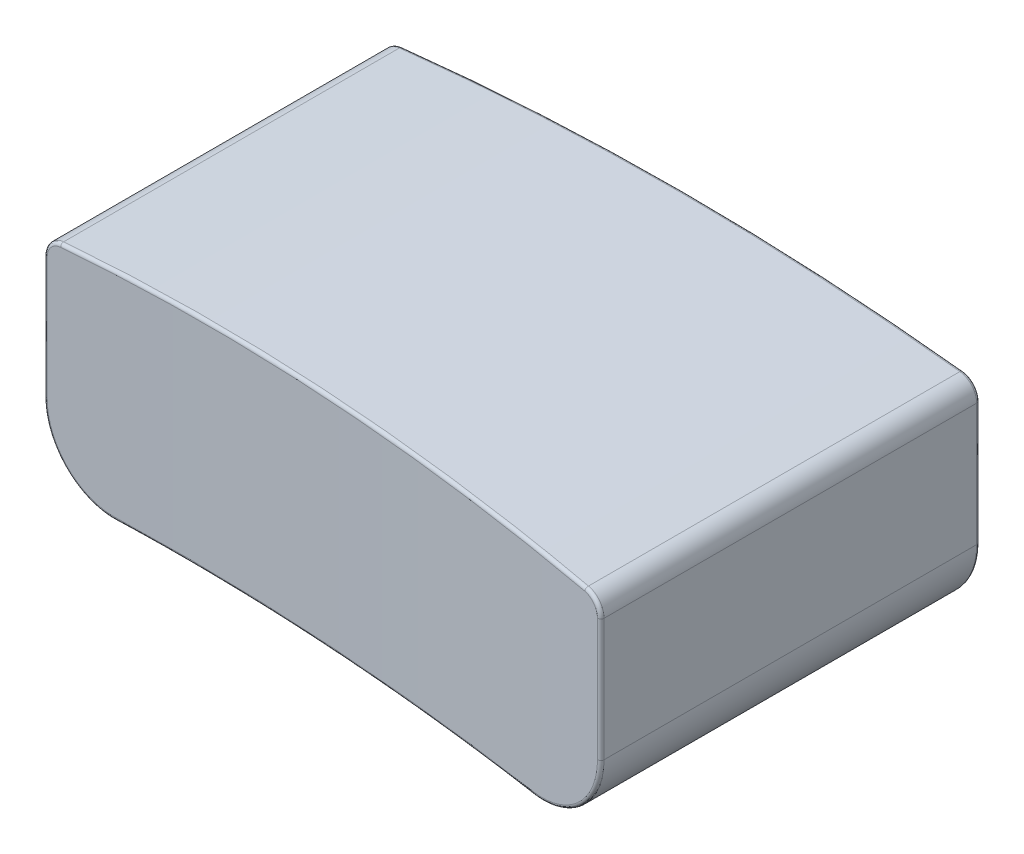
SolidWorks part; units mm, degrees
ref_plane "Front Plane" through (0, 0, 0) normal (0, 0, 1) x (1, 0, 0)
ref_plane "Top Plane" through (0, 0, 0) normal (0, 1, 0) x (1, 0, 0)
ref_plane "Right Plane" through (0, 0, 0) normal (1, 0, 0) x (0, 0, -1)
sketch "Sketch1" plane through (0, 0, 0) normal (0, 0, 1) x (1, 0, 0)
  line L0 (55, 0) -> (-55, 0) construction
  line L1 (-4.7, 1.85) -> (4.7, 1.85)
  line L2 (-4.7, 1.85) -> (-4.7, -1.85)
  line L3 (-4.7, -1.85) -> (4.7, -1.85)
  line L4 (4.7, 1.85) -> (4.7, -1.85)
  line L5 (0, -55) -> (0, 55) construction
  dimension "D1" = 9.4
  dimension "D2" = 3.7
  dimension "D3" = 1.85
  dimension "D4" = 4.7
extrude "Boss-Extrude1" add sketch "Sketch1" along normal mid plane 6
sketch "Sketch2" plane through (0, 0, 3) normal (0, 0, 1) x (1, 0, 0)
  line L0 (-4.7, 1.85) -> (-4.7, -1.85) construction
  line L1 (4.7, -1.85) -> (4.7, 1.85) construction
  line L2 (-4.7, -1.85) -> (4.7, -1.85) construction
  line L3 (4.7, 1.85) -> (-4.7, 1.85) construction
  line L4 (-4.7, 1.55) -> (-7.1207, 4.0114)
  line L5 (-7.1207, 4.0114) -> (5.5359, 3.8867)
  line L6 (5.5359, 3.8867) -> (4.7, 1.55)
  line L7 (4.7, -1.85) -> (0.3506, -3.782)
  line L8 (-4.7, -1.85) -> (0.3506, -3.782)
  arc A0 (-4.7, 1.55) -> (4.7, 1.55) centre (0, -38.1729) cw
  arc A1 (-4.7, -1.85) -> (4.7, -1.85) centre (0, -51.6286) cw
  dimension "D4" = 40
  dimension "D5" = 50
  dimension "D1" = 0
  dimension "D2" = 0.3
  dimension "D3" = 0.3
extrude "Cut-Extrude1" cut sketch "Sketch2" against normal mid plane 15.6
fillet "Fillet1" radius 1.1 2 edges at (4.7, -1.85, 0) (-4.7, -1.85, 0)
fillet "Fillet2" radius 0.3 2 edges at (4.7, 1.55, 0) (-4.7, 1.55, 0)
sketch "Sketch3" plane through (0, 0, 3) normal (0, 0, 1) x (1, 0, 0)
  line L0 (0, -2.7889) -> (0, 2.7889) construction
  line L1 (3.8449, 0) -> (-3.8449, 0) construction
  circle A0 centre (3.1, -0.6) radius 0.5
  circle A1 centre (-3.1, -0.6) radius 0.5
  dimension "D1" = 1
  dimension "D2" = 3.1
  dimension "D3" = 1
  dimension "D5" = 0.6
  dimension "D6" = 0.6
  dimension "D4" = 3.1
extrude "Cut-Extrude2" cut sketch "Sketch3" against normal blind 13 from offset 2 offset against normal yes
fillet "Fillet4" radius 0.02 2 edges at (3.6, -0.6, -3) (-2.6, -0.6, -3)
sketch "Sketch4" plane through (0, 0, 0) normal (0, 1, 0) x (1, 0, 0)
  line L1 (4.4332, 3) -> (-4.4332, 3) construction
  line L2 (0, -2.7889) -> (0, 2.7889) construction
  line L8 (6.4207, -4.7741) -> (4.7, -3)
  line L9 (-6.6127, -3.9139) -> (6.4207, -4.7741)
  line L10 (-4.7, -2.4) -> (-6.6127, -3.9139)
  arc A1 (4.7, -3) -> (-4.7, -2.4) centre (-9.5503, -152.3216) ccw
  dimension "D3" = 150
  dimension "D1" = 5.4
  dimension "D2" = 6
  dimension "D4" = 4.7
extrude "Cut-Extrude3" cut sketch "Sketch4" against normal mid plane 10
fillet "Fillet5" radius 0.05 17 edges at (-4.7, 0.3135, -3) (-4.3499, -1.4603, -3) (0, -1.6286, -3) (4.3499, -1.4603, -3) (4.7, 0.3135, -3) (4.7, 0.3135, 3) (4.2273, -1.5592, 2.9556) (-4.4592, -1.3425, 2.408) (-4.7, 0.3135, 2.4) (4.6348, 1.4693, 2.9938) (3.6, -0.6, 1) (0, 1.8271, -3) (-4.6236, 1.4825, -3) (4.6236, 1.4825, -3) (-4.6123, 1.4945, 2.4029)
sketch "Sketch5" plane through (0, 0, 0) normal (0, 1, 0) x (1, 0, 0)
  line L0 (3.526, 3) -> (-3.526, 3) construction
  line L1 (-4.7, 2.95) -> (-4.7, -2.3516) construction
  circle A0 centre (-0.7, 1.5) radius 0.4
  dimension "D1" = 0.8
  dimension "D2" = 1.5
  dimension "D3" = 4
extrude "Cut-Extrude4" cut sketch "Sketch5" along normal offset from surface (8.7665 mm away) 0.4 from offset 10 offset against normal yes
fillet "Fillet6" radius 0.05 1 edges at (-0.792, -1.6349, -1.1107)
